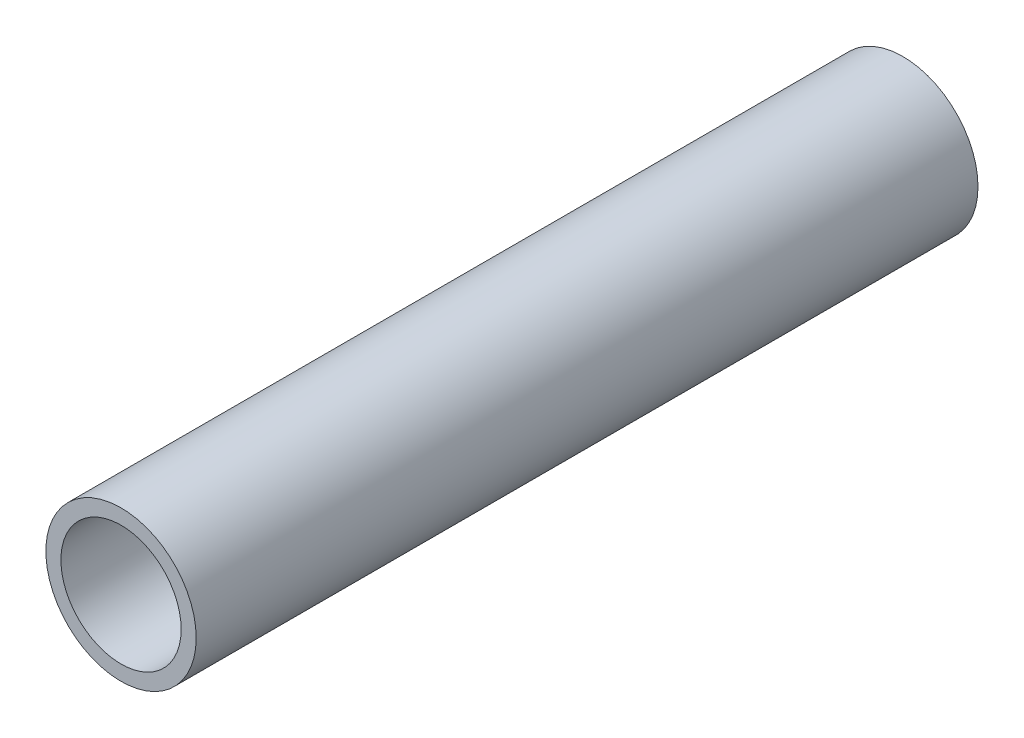
SolidWorks part; units mm, degrees
ref_plane "Front Plane" through (0, 0, 0) normal (0, 0, 1) x (1, 0, 0)
ref_plane "Top Plane" through (0, 0, 0) normal (0, 1, 0) x (1, 0, 0)
ref_plane "Right Plane" through (0, 0, 0) normal (1, 0, 0) x (0, 0, -1)
sketch "Sketch1" plane through (0, 0, 0) normal (0, 0, 1) x (1, 0, 0)
  circle A0 centre (0, 0) radius 1.25
  circle A1 centre (0, 0) radius 1
extrude "Boss-Extrude1" add sketch "Sketch1" along normal blind 13
equation "\"D1@Boss-Extrude1\"= 13 'Tube DIP Length"
